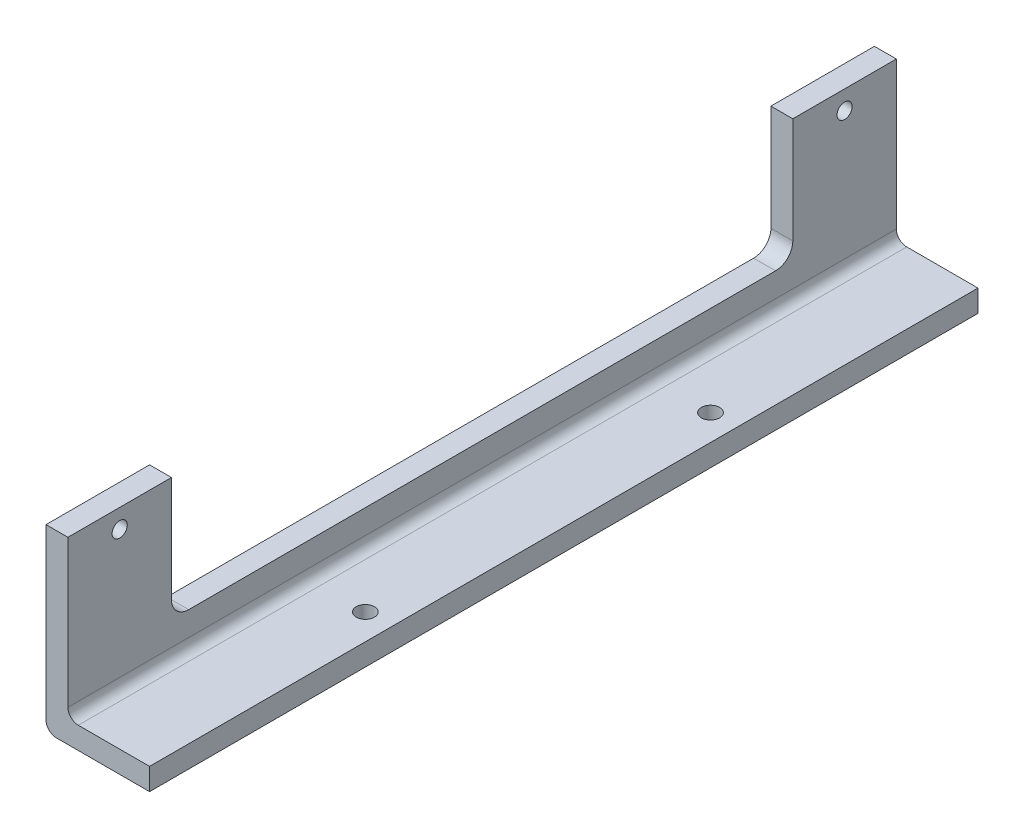
SolidWorks part; units mm, degrees
material "6061-T6 Al"
ref_plane "Front Plane" through (0, 0, 0) normal (0, 0, 1) x (1, 0, 0)
ref_plane "Top Plane" through (0, 0, 0) normal (0, 1, 0) x (1, 0, 0)
ref_plane "Right Plane" through (0, 0, 0) normal (1, 0, 0) x (0, 0, -1)
sketch "Sketch1" plane through (0, 0, 0) normal (0, 0, 1) x (1, 0, 0)
  line L0 (0, 0) -> (50.8, 0)
  line L1 (0, 0) -> (0, 55)
  dimension "D1" = 55
  dimension "D2" = 50.8
extrude "Extrude-Thin1" add sketch "Sketch1" against normal blind 240 thin thin type one direction wall 6.35
sketch "Sketch3" plane through (0, 6.35, 0) normal (0, 1, 0) x (1, 0, 0)
  line L0 (0, 240) -> (0, 0) construction
  line L1 (30, 245) -> (65, 245)
  line L2 (30, 245) -> (30, -55)
  line L3 (30, -55) -> (65, -55)
  line L4 (65, 245) -> (65, -55)
  line L5 (50.8, 240) -> (6.35, 240) construction
  dimension "D1" = 30
  dimension "D2" = 35
  dimension "D3" = 5
  dimension "D4" = 300
extrude "Extrude2" cut sketch "Sketch3" against normal through all
sketch "Sketch4" plane through (0, 6.35, 0) normal (0, 1, 0) x (1, 0, 0)
  line L0 (30, 240) -> (6.35, 240) construction
  line L1 (30, 240) -> (30, 0) construction
  line L2 (20.25, 172.25) -> (24.75, 172.25)
  line L3 (20.25, 167.75) -> (24.75, 167.75)
  line L4 (-3.0451, 120) -> (27.5098, 120) construction
  line L5 (20.25, 67.75) -> (24.75, 67.75)
  line L6 (20.25, 72.25) -> (24.75, 72.25)
  line L7 (30, 0) -> (6.35, 0) construction
  circle A0 centre (22.5, 170) radius 2.25 construction
  circle A1 centre (22.5, 70) radius 2.25 construction
  arc A2 (20.25, 172.25) -> (20.25, 167.75) centre (20.25, 170) ccw
  arc A3 (24.75, 167.75) -> (24.75, 172.25) centre (24.75, 170) ccw
  arc A4 (20.25, 67.75) -> (20.25, 72.25) centre (20.25, 70) cw
  arc A5 (24.75, 72.25) -> (24.75, 67.75) centre (24.75, 70) cw
  circle A6 centre (22.5, 170) radius 2 construction
  dimension "D3" = 4.5
  dimension "D7" = 4
  dimension "D8" = 2.5
  dimension "D9" = 3
  dimension "D1" = 100
  dimension "D2" = 70
  dimension "D4" = 7.5
  dimension "D5" = 4.5
  dimension "D6" = 2.25
  dimension "D10" = 70
sketch "Sketch7" plane through (6.35, 0, 0) normal (1, 0, 0) x (0, 0, -1)
  line L0 (240, 0) -> (0, 0) construction
  line L1 (-5, 82) -> (295, 82)
  line L2 (-5, 82) -> (-5, 52)
  line L3 (-5, 52) -> (295, 52)
  line L4 (295, 82) -> (295, 52)
  line L5 (0, 6.35) -> (0, 55) construction
  dimension "D1" = 52
  dimension "D2" = 30
  dimension "D3" = 5
  dimension "D4" = 300
extrude "Extrude4" cut sketch "Sketch7" against normal through all
sketch "Sketch10" plane through (6.35, 0, 0) normal (1, 0, 0) x (0, 0, -1)
  line L0 (0, 6.35) -> (0, 52) construction
  line L1 (30, 66.35) -> (210, 66.35)
  line L2 (30, 66.35) -> (30, 21.35)
  line L3 (35, 16.35) -> (205, 16.35)
  line L4 (210, 66.35) -> (210, 21.35)
  line L7 (240, 0) -> (0, 0) construction
  line L8 (240, 6.35) -> (240, 52) construction
  arc A0 (35, 16.35) -> (30, 21.35) centre (35, 21.35) cw
  arc A1 (210, 21.35) -> (205, 16.35) centre (205, 21.35) cw
  dimension "D6" = 5
  dimension "D1" = 30
  dimension "D2" = 30
  dimension "D4" = 50
  dimension "D5" = 16.35
extrude "Extrude5" cut sketch "Sketch10" against normal through all
hole_wizard "Tapped Hole for #8-32 Helicoil1" positions "3DSketch3" profile "Sketch32" tap size "#8-32" standard "Helicoil® Inch" end condition through all
sketch3d "3DSketch3"
  line L1 (6.35, 6.35, 0) -> (6.35, 52, 0) construction
  line L2 (6.35, 6.35, -240) -> (6.35, 52, -240) construction
  line L4 (6.35, 52, 0) -> (6.35, 52, -30) construction
  point P6 (6.35, 46.5, -15)
  point P8 (6.35, 46.5, -225)
  dimension "D1" = 5.5
  dimension "D2" = 15
  dimension "D3" = 15
cosmetic thread "Hole Thread3" parameters "D1"=5.08, "D2"=5.2756
cosmetic thread "Hole Thread4" parameters "D1"=5.08, "D2"=5.2756
sketch "Sketch32" plane through (6.35, 46.5, -15) normal (0, 1, 0) x (0, 0, -1)
  line L0 (0, 0) -> (0, 6.35)
  line L1 (0, 6.35) -> (2.1971, 6.35)
  line L2 (2.1971, 6.35) -> (2.1971, 0)
  line L5 (2.1971, 0) -> (0, 0)
  line L11 (0, -6.35) -> (0, 107.95) construction
  dimension "Thru Tap Drill Dia." = 4.3942
  dimension "Thru Tap Drill Depth" = 6.35
sketch "Sketch14" plane through (0, 6.35, 0) normal (0, 1, 0) x (1, 0, 0)
  circle A0 centre (22.5, 70) radius 2.25 construction
  circle A1 centre (22.5, 170) radius 2.25 construction
  circle A2 centre (22.5, 70) radius 2.25
  circle A3 centre (22.5, 170) radius 2.25
hole_wizard "Tapped Hole for #8-32 Helicoil2" positions "3DSketch4" profile "Sketch33" tap size "#8-32" standard "Helicoil® Inch"
sketch3d "3DSketch4"
  point P0 (22.5, 6.35, -70)
  point P3 (22.5, 6.35, -170)
sketch "Sketch33" plane through (22.5, 6.35, -70) normal (1, 0, 0) x (0, 0, 1)
  line L0 (0, 0) -> (0, 12.4454)
  line L1 (0, 12.4454) -> (2.1971, 11.1252)
  line L2 (2.1971, 11.1252) -> (2.1971, 5.08)
  line L3 (2.1971, 5.08) -> (2.6378, 5.08)
  line L4 (2.6378, 5.08) -> (2.6378, 0)
  line L5 (2.6378, 0) -> (0, 0)
  line L10 (0, 12.4454) -> (-2.1971, 11.1252) construction
  line L11 (0, -6.35) -> (0, 107.95) construction
  dimension "Tap Drill Dia." = 4.3942
  dimension "Tap Drill Depth" = 11.1252
  dimension "Thread Major Dia." = 5.2756
  dimension "Thread Depth" = 5.08
  dimension "Drill Angle" = 118
fillet "Fillet5" radius 3 2 edges at (0, 0, -120) (6.35, 6.35, -120)
